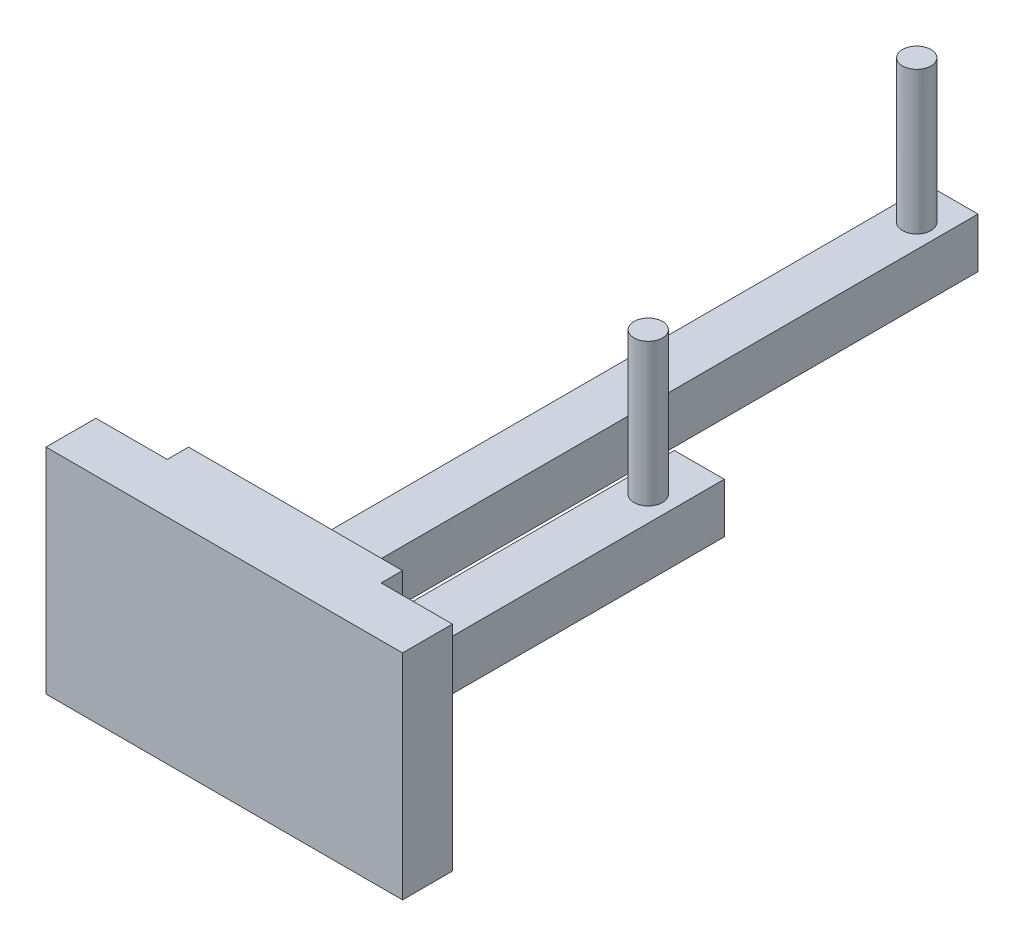
SolidWorks part; units mm, degrees
ref_plane "Front Plane" through (0, 0, 0) normal (0, 0, 1) x (1, 0, 0)
ref_plane "Top Plane" through (0, 0, 0) normal (0, 1, 0) x (1, 0, 0)
ref_plane "Right Plane" through (0, 0, 0) normal (1, 0, 0) x (0, 0, -1)
sketch "Sketch1" plane through (0, 0, 0) normal (0, 0, 1) x (1, 0, 0)
  line L1 (-15, 15) -> (15, 15)
  line L2 (-15, 15) -> (-15, -15)
  line L3 (-15, -15) -> (15, -15)
  line L4 (15, 15) -> (15, -15)
  line L5 (-15, 15) -> (15, -15) construction
  line L6 (-15, -15) -> (15, 15) construction
  line L7 (-25, -15) -> (25, -15)
  line L8 (-25, -15) -> (-25, 15)
  line L9 (-25, 15) -> (25, 15)
  line L10 (25, -15) -> (25, 15)
  line L11 (-25, -15) -> (25, 15) construction
  line L12 (-25, 15) -> (25, -15) construction
  point P1 (0, 0)
  point P6 (0, 0)
  dimension "D1" = 30
  dimension "D2" = 30
  dimension "D3" = 50
extrude "Boss-Extrude4" add sketch "Sketch1" along normal blind 7 contours L9 L8 L7 L2 | L4 L1 L2 L3 | L7 L10 L9 L4
sketch "Sketch3" plane through (0, 0, 0) normal (0, 0, -1) x (-1, 0, 0)
  line L0 (25, 15) -> (-25, 15) construction
  line L1 (15, -15) -> (-15, -15)
  line L2 (15, -15) -> (15, 15)
  line L3 (15, 15) -> (-15, 15)
  line L4 (-15, -15) -> (-15, 15)
  line L5 (15, -15) -> (-15, 15) construction
  line L6 (15, 15) -> (-15, -15) construction
  point P0 (0, 0)
  dimension "D1" = 30
extrude "Boss-Extrude5" add sketch "Sketch3" along normal blind 3
sketch "Sketch4" plane through (0, 0, -3) normal (0, 0, -1) x (-1, 0, 0)
  line L1 (-3.1209, -8.3489) -> (-10.1209, -8.3489)
  line L2 (-3.1209, -8.3489) -> (-3.1209, -1.3489)
  line L3 (-3.1209, -1.3489) -> (-10.1209, -1.3489)
  line L4 (-10.1209, -8.3489) -> (-10.1209, -1.3489)
  line L5 (-3.1209, -8.3489) -> (-10.1209, -1.3489) construction
  line L6 (-3.1209, -1.3489) -> (-10.1209, -8.3489) construction
  point P0 (-6.6209, -4.8489)
  dimension "D1" = 7
  dimension "D2" = 7
extrude "Boss-Extrude8" add sketch "Sketch4" along normal blind 50
sketch "Sketch6" plane through (0, -1.3489, 0) normal (0, 1, 0) x (1, 0, 0)
  line L0 (6.6209, 53) -> (6.6209, -26.3517) construction
  line L1 (3.1209, 53) -> (10.1209, 53) construction
  circle A0 centre (6.6209, 45.8378) radius 2
extrude "Boss-Extrude9" add sketch "Sketch6" along normal blind 20
sketch "Sketch7" plane through (0, 0, -3) normal (0, 0, -1) x (-1, 0, 0)
  line L0 (-3.1209, -8.3489) -> (14.0263, -8.3489) construction
  line L1 (-3.1209, -4.8489) -> (15, -4.8489) construction
  line L2 (-3.1209, -8.3489) -> (-3.1209, -1.3489) construction
  line L3 (15, -15) -> (15, 15) construction
  line L5 (4.2963, -8.3489) -> (11.2963, -8.3489)
  line L6 (4.2963, -8.3489) -> (4.2963, -1.3489)
  line L7 (4.2963, -1.3489) -> (11.2963, -1.3489)
  line L8 (11.2963, -8.3489) -> (11.2963, -1.3489)
  line L9 (4.2963, -8.3489) -> (11.2963, -1.3489) construction
  line L10 (4.2963, -1.3489) -> (11.2963, -8.3489) construction
  point P9 (7.7963, -4.8489)
  dimension "D1" = 7
  dimension "D2" = 7
extrude "Boss-Extrude13" add sketch "Sketch7" along normal blind 100
sketch "Sketch10" plane through (0, -1.3489, 0) normal (0, 1, 0) x (1, 0, 0)
  circle A0 centre (-7.5834, 97.696) radius 2
extrude "Boss-Extrude14" add sketch "Sketch10" along normal blind 20
